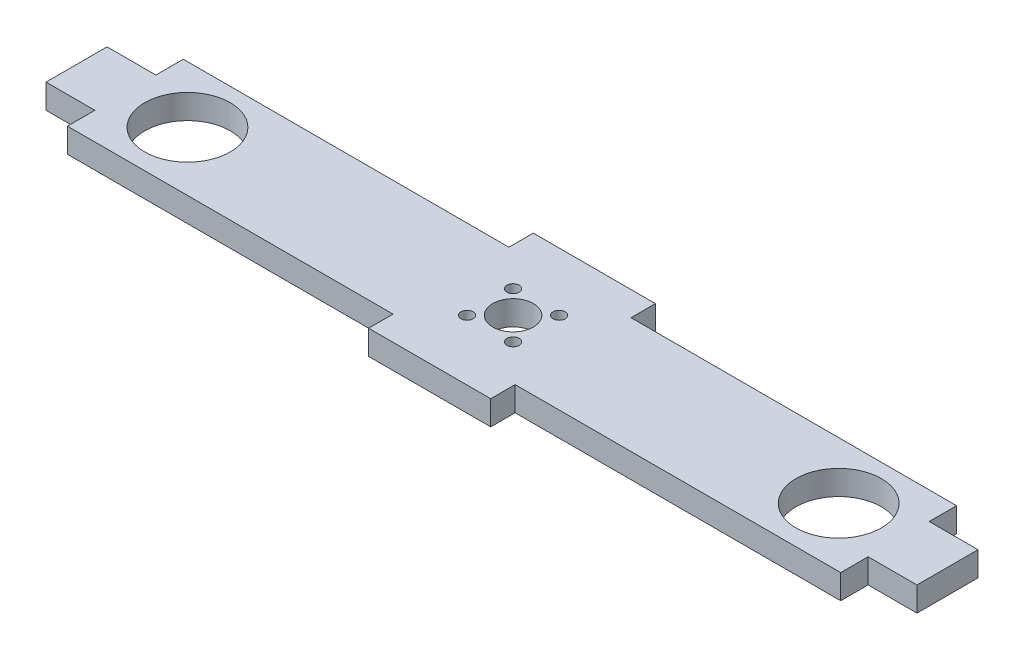
SolidWorks part; units mm, degrees
ref_plane "Front" through (0, 0, 0) normal (0, 0, 1) x (1, 0, 0)
ref_plane "Top" through (0, 0, 0) normal (0, 1, 0) x (1, 0, 0)
ref_plane "Right" through (0, 0, 0) normal (1, 0, 0) x (0, 0, -1)
sketch "Эскиз1" plane through (0, 0, 0) normal (0, 1, 0) x (1, 0, 0)
  line L0 (110.5788, 0.265) -> (-105.6913, 0.265) construction
  line L1 (-95, 14.235) -> (-15, 14.235)
  line L2 (-95, 14.235) -> (-95, 7.5)
  line L3 (-95, -14.235) -> (-15, -14.235)
  line L4 (95, 14.235) -> (95, 7.5)
  line L5 (-95, 14.235) -> (95, -14.235) construction
  line L6 (-95, -14.235) -> (95, 14.235) construction
  line L7 (-80, 48.7611) -> (-80, -31.1923) construction
  line L8 (80, 43.1247) -> (80, -42.2563) construction
  line L9 (0, 43.1247) -> (0, -49.9803) construction
  line L10 (-98.4497, 20.235) -> (101.9556, 20.235) construction
  line L11 (-98.4497, -20.235) -> (110.5788, -20.235) construction
  line L12 (15, 14.235) -> (95, 14.235)
  line L13 (-15, 20.235) -> (15, 20.235)
  line L14 (-15, 20.235) -> (-15, 14.235)
  line L16 (15, 20.235) -> (15, 14.235)
  line L17 (15, -14.235) -> (95, -14.235)
  line L19 (-15, -14.235) -> (-15, -20.235)
  line L20 (-15, -20.235) -> (15, -20.235)
  line L21 (15, -14.235) -> (15, -20.235)
  line L22 (0, 0) -> (111.9405, 0) construction
  line L23 (95, 7.5) -> (107, 7.5)
  line L27 (107, 7.5) -> (107, -7.5)
  line L28 (95, -7.5) -> (95, -14.235)
  line L29 (-95, -7.5) -> (-107, -7.5)
  line L30 (-107, 7.5) -> (-107, -7.5)
  line L31 (95, -7.5) -> (107, -7.5)
  line L32 (-95, 7.5) -> (-107, 7.5)
  line L33 (-95, -7.5) -> (-95, -14.235)
  line L39 (-5.6569, -5.3919) -> (5.6569, 5.9219) construction
  line L40 (-5.6569, 5.9219) -> (5.6569, -5.3919) construction
  circle A1 centre (-80, 0.265) radius 10.5
  circle A2 centre (80, 0.265) radius 10.5
  circle A3 centre (0, 0.265) radius 5
  circle A4 centre (-5.6569, 5.9219) radius 1.5
  circle A5 centre (5.6569, 5.9219) radius 1.5
  circle A6 centre (5.6569, -5.3919) radius 1.5
  circle A7 centre (-5.6569, -5.3919) radius 1.5
  point P0 (0, 0)
  point P24 (0, 14.235)
  point P25 (0, -14.235)
  point P36 (95, 0)
  dimension "D4" = 10
  dimension "D7" = 21
  dimension "D18" = 3
  dimension "D17" = 8
  dimension "D19" = 16
  dimension "D20" = 8
  dimension "D21" = 16
  dimension "D1" = 190
  dimension "D2" = 28.47
  dimension "D3" = 13.97
  dimension "D5" = 15
  dimension "D6" = 15
  dimension "D8" = 6
  dimension "D9" = 6
  dimension "D10" = 30
  dimension "D11" = 30
  dimension "D12" = 15
  dimension "D13" = 15
  dimension "D14" = 15
  dimension "D15" = 12
  dimension "D16" = 7.5
extrude "Бобышка-Вытянуть1" add sketch "Эскиз1" along normal blind 6
